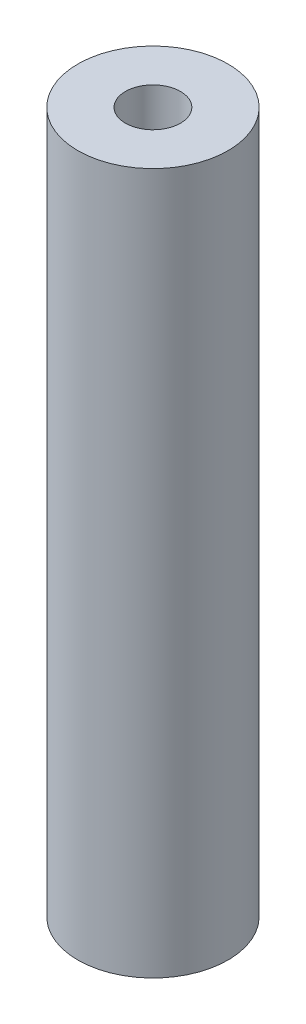
SolidWorks part; units mm, degrees
ref_plane "Front Plane" through (0, 0, 0) normal (0, 0, 1) x (1, 0, 0)
ref_plane "Top Plane" through (0, 0, 0) normal (0, 1, 0) x (1, 0, 0)
ref_plane "Right Plane" through (0, 0, 0) normal (1, 0, 0) x (0, 0, -1)
sketch "Sketch1" plane through (0, 952.6882, 0) normal (0, 1, 0) x (1, 0, 0)
  circle A0 centre (738.2581, -1161.2145) radius 7.5
  circle A1 centre (738.2581, -1161.2145) radius 2.75 construction
  circle A2 centre (738.2581, -1161.2145) radius 2.75
  dimension "D1" = 15
extrude "Boss-Extrude1" add sketch "Sketch1" along normal blind 70
